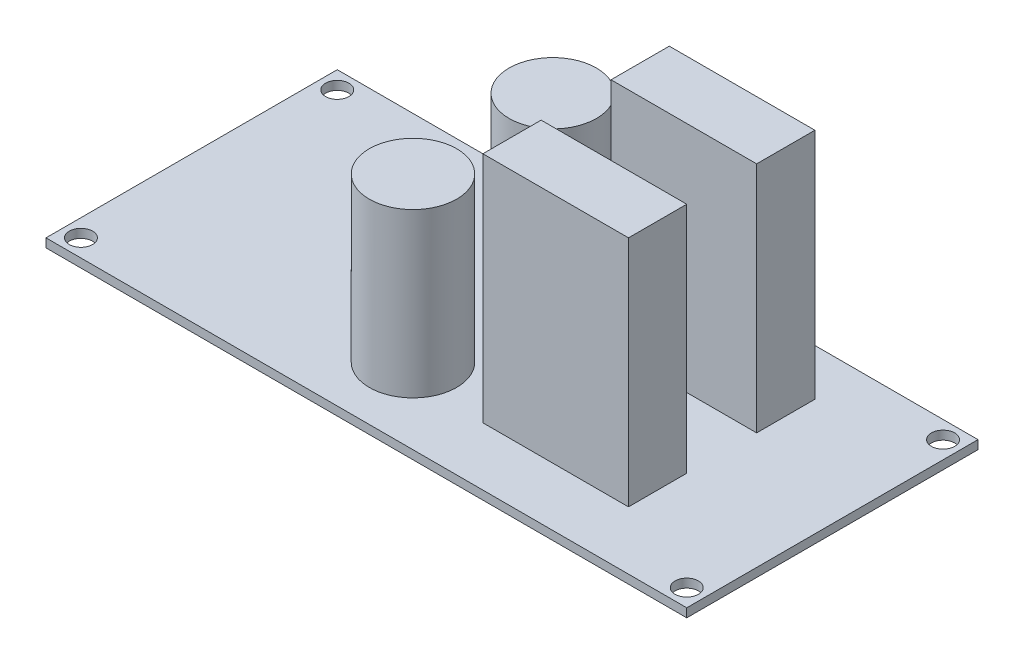
SolidWorks part; units mm, degrees
ref_plane "Plano frontal" through (0, 0, 0) normal (0, 0, 1) x (1, 0, 0)
ref_plane "Plano superior" through (0, 0, 0) normal (0, 1, 0) x (1, 0, 0)
ref_plane "Plano direito" through (0, 0, 0) normal (1, 0, 0) x (0, 0, -1)
sketch "Esboço1" plane through (0, 0, 0) normal (0, 1, 0) x (1, 0, 0)
  line L1 (0, 0) -> (110, 0)
  line L2 (0, 0) -> (0, 50)
  line L3 (0, 50) -> (110, 50)
  line L4 (110, 0) -> (110, 50)
  dimension "D1" = 110
  dimension "D2" = 50
extrude "Ressalto-extrusão1" add sketch "Esboço1" along normal blind 1.5
sketch "Esboço2" plane through (0, 1.5, 0) normal (0, 1, 0) x (1, 0, 0)
  line L0 (110, 0) -> (110, 50) construction
  line L1 (0, 50) -> (0, 0) construction
  line L2 (0, 0) -> (110, 0) construction
  line L3 (110, 50) -> (0, 50) construction
  circle A0 centre (107, 3) radius 2
  circle A1 centre (107, 47) radius 2
  circle A2 centre (3, 3) radius 2
  circle A3 centre (3, 47) radius 2
  dimension "D1" = 4
  dimension "D2" = 4
  dimension "D3" = 4
  dimension "D4" = 4
  dimension "D5" = 3
  dimension "D6" = 3
  dimension "D7" = 3
  dimension "D8" = 3
  dimension "D9" = 3
  dimension "D10" = 3
  dimension "D11" = 3
  dimension "D12" = 3
extrude "Corte-extrusão1" cut sketch "Esboço2" against normal blind 1.5
sketch "Esboço4" plane through (0, 1.5, 0) normal (0, 1, 0) x (1, 0, 0)
  line L1 (110, 50) -> (0, 50) construction
  line L2 (0, 0) -> (110, 0) construction
  line L3 (0, 50) -> (0, 0) construction
  line L4 (110, 0) -> (110, 50) construction
  line L5 (90, 42) -> (65, 42)
  line L6 (90, 42) -> (90, 32)
  line L7 (90, 32) -> (65, 32)
  line L8 (65, 42) -> (65, 32)
  line L9 (90, 20) -> (65, 20)
  line L10 (90, 20) -> (90, 10)
  line L11 (90, 10) -> (65, 10)
  line L12 (65, 20) -> (65, 10)
  circle A0 centre (50, 37) radius 7.5
  circle A1 centre (50, 13) radius 7.5
  dimension "D1" = 15
  dimension "D2" = 15
  dimension "D3" = 13
  dimension "D4" = 13
  dimension "D5" = 50
  dimension "D6" = 50
  dimension "D7" = 25
  dimension "D8" = 25
  dimension "D9" = 10
  dimension "D10" = 10
  dimension "D11" = 8
  dimension "D12" = 10
  dimension "D13" = 20
  dimension "D14" = 20
extrude "Ressalto-extrusão3" add sketch "Esboço4" along normal blind 40
sketch "Esboço5" plane through (0, 0, 0) normal (1, 0, 0) x (0, 0, -1)
  line L0 (5.5, 41.5) -> (5.5, 1.5) construction
  line L1 (44.5, 41.5) -> (5.5, 41.5)
  line L2 (44.5, 41.5) -> (44.5, 29.5)
  line L3 (44.5, 29.5) -> (5.5, 29.5)
  line L4 (5.5, 41.5) -> (5.5, 29.5)
  dimension "D1" = 12
extrude "Corte-extrusão2" cut sketch "Esboço5" along normal blind 60
